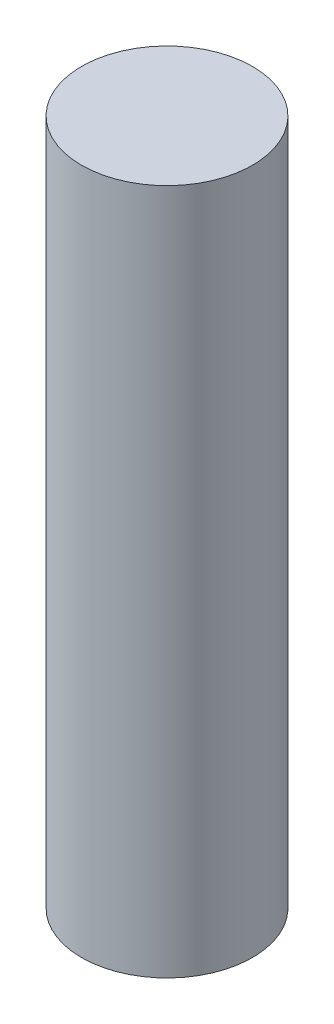
SolidWorks part; units mm, degrees
material "Plain Carbon Steel"
ref_plane "Front Plane" through (0, 0, 0) normal (0, 0, 1) x (1, 0, 0)
ref_plane "Top Plane" through (0, 0, 0) normal (0, 1, 0) x (1, 0, 0)
ref_plane "Right Plane" through (0, 0, 0) normal (1, 0, 0) x (0, 0, -1)
sketch "Sketch1" plane through (0, 0, 0) normal (0, 1, 0) x (1, 0, 0)
  circle A0 centre (0, 0) radius 2.3749
  dimension "D1" = 4.7498
extrude "Boss-Extrude1" add sketch "Sketch1" along normal blind 19.05
